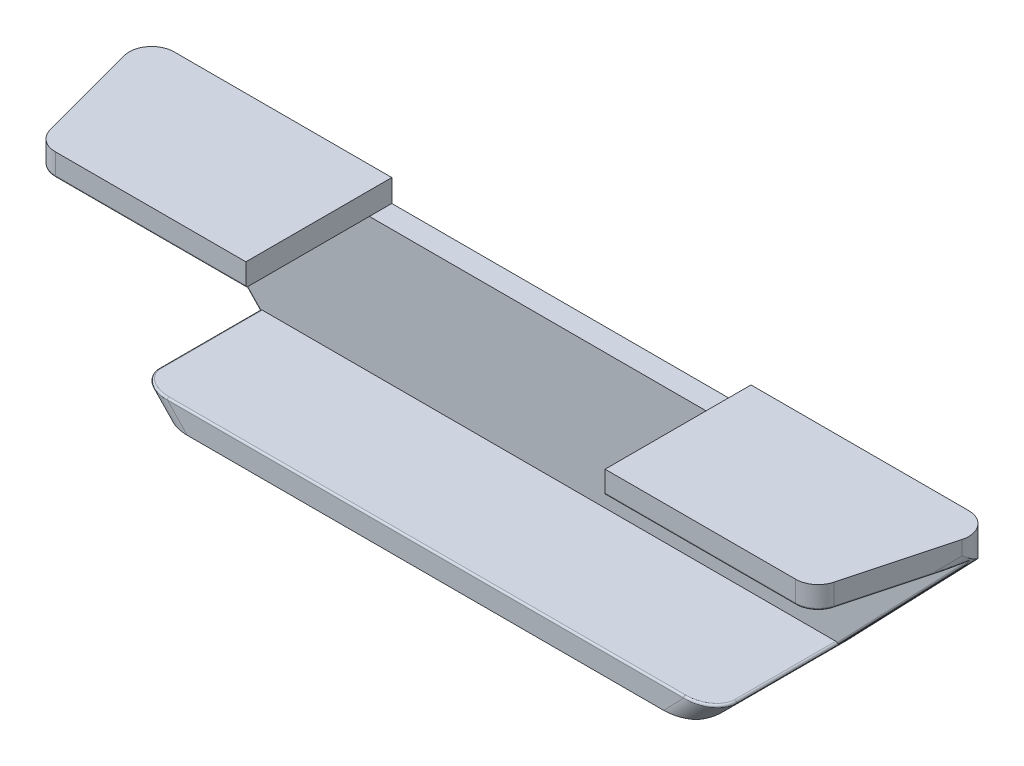
SolidWorks part; units mm, degrees
material "1060 Alloy"
ref_plane "Front Plane" through (0, 0, 0) normal (0, 0, 1) x (1, 0, 0)
ref_plane "Top Plane" through (0, 0, 0) normal (0, 1, 0) x (1, 0, 0)
ref_plane "Right Plane" through (0, 0, 0) normal (1, 0, 0) x (0, 0, -1)
sketch "Sketch1" plane through (0, 0, 0) normal (1, 0, 0) x (0, 0, -1)
  line L0 (3.175, 22.225) -> (22.225, 22.225)
  line L1 (0, 0) -> (25.4, 0)
  line L2 (0, 0) -> (0, 25.4)
  line L3 (0, 25.4) -> (25.4, 25.4)
  line L4 (25.4, 0) -> (25.4, 25.4)
  line L5 (22.225, 3.175) -> (22.225, 22.225)
  line L6 (3.175, 3.175) -> (22.225, 3.175)
  line L7 (3.175, 3.175) -> (3.175, 22.225)
  dimension "D1" = 25.4
  dimension "D2" = 3.175
extrude "Boss-Extrude1" add sketch "Sketch1" along normal blind 120.65
sketch "Sketch2" plane through (0, 25.4, 0) normal (0, 1, 0) x (1, 0, 0)
  line L0 (0, 25.4) -> (5.5298, 4.7625)
  line L1 (5.5298, 4.7625) -> (115.1202, 4.7625)
  line L2 (115.1202, 4.7625) -> (120.65, 25.4)
  line L3 (120.65, 25.4) -> (120.65, 0)
  line L4 (120.65, 0) -> (0, 0)
  line L5 (0, 0) -> (0, 25.4)
  line L6 (120.65, 25.4) -> (0, 25.4) construction
  dimension "D1" = 20.6375
  dimension "D2" = 15
  dimension "D3" = 15
extrude "Cut-Extrude1" cut sketch "Sketch2" against normal through all
sketch "Sketch3" plane through (0, 0, -4.7625) normal (0, 0, 1) x (1, 0, 0)
  line L0 (0.8507, 22.225) -> (22.225, 0)
  line L1 (115.1202, 0) -> (5.5298, 0) construction
  line L2 (22.225, 0) -> (0, 0)
  line L3 (0, 0) -> (0, 23.1096)
  line L4 (0, 0) -> (0, 25.4) construction
  line L5 (0, 23.1096) -> (0.8507, 22.225)
  line L6 (120.65, 23.1096) -> (119.7993, 22.225)
  line L7 (120.65, 0) -> (120.65, 25.4) construction
  line L8 (119.7993, 22.225) -> (98.425, 0)
  line L9 (98.425, 0) -> (120.65, 0)
  line L10 (120.65, 0) -> (120.65, 23.1096)
  dimension "D1" = 76.2
extrude "Cut-Extrude2" cut sketch "Sketch3" against normal through all
fillet "Fillet1" radius 3.175 10 edges at (99.9517, 1.5875, -4.7625) (20.6983, 1.5875, -4.7625) (22.225, 0, -15.0813) (98.425, 0, -15.0813) (120.65, 24.2548, -25.4) (120.2246, 22.6673, -23.8125) (0, 24.2548, -25.4) (0.4254, 22.6673, -23.8125) (115.1202, 23.8125, -4.7625) (5.5298, 23.8125, -4.7625)
fillet "Fillet2" radius 0.254 16 edges at (119.1963, 21.6765, -22.225) (1.5849, 22.225, -19.7673) (119.0651, 22.225, -19.7673) (117.1059, 22.225, -12.1732) (114.6168, 22.225, -5.4186) (60.325, 22.225, -4.7625) (6.0332, 22.225, -5.4186) (1.4537, 21.6765, -22.225) (101.4785, 3.175, -15.0813) (100.1883, 3.175, -5.6924) (19.1715, 3.175, -15.0813) (20.4617, 3.175, -5.6924) (110.1396, 12.1808, -22.225) (3.5441, 22.225, -12.1732) (10.5104, 12.1808, -22.225) (60.325, 3.175, -4.7625)
sketch "Sketch4" plane through (0, 0, -22.225) normal (0, 0, 1) x (1, 0, 0)
  line L0 (60.325, 22.225) -> (60.325, 12.7) construction
  line L1 (119.2508, 22.225) -> (1.3992, 22.225) construction
  line L2 (22.225, 12.7) -> (98.425, 12.7) construction
  circle A0 centre (22.225, 12.7) radius 1.75
  circle A1 centre (98.425, 12.7) radius 1.75
  dimension "D3" = 3.5
  dimension "D1" = 12.7
  dimension "D2" = 76.2
extrude "Cut-Extrude3" cut sketch "Sketch4" against normal through all
sketch "Sketch5" plane through (0, 25.4, 0) normal (0, 1, 0) x (1, 0, 0)
  line L0 (116.5123, 25.4) -> (4.1377, 25.4) construction
  line L1 (34.925, 25.4) -> (85.725, 25.4)
  line L2 (34.925, 25.4) -> (34.925, 4.7625)
  line L3 (34.925, 4.7625) -> (85.725, 4.7625)
  line L4 (85.725, 25.4) -> (85.725, 4.7625)
  line L5 (112.6839, 4.7625) -> (7.9661, 4.7625) construction
  point P8 (60.325, 25.4)
  dimension "D1" = 50.8
extrude "Cut-Extrude4" cut sketch "Sketch5" against normal blind 3.175
